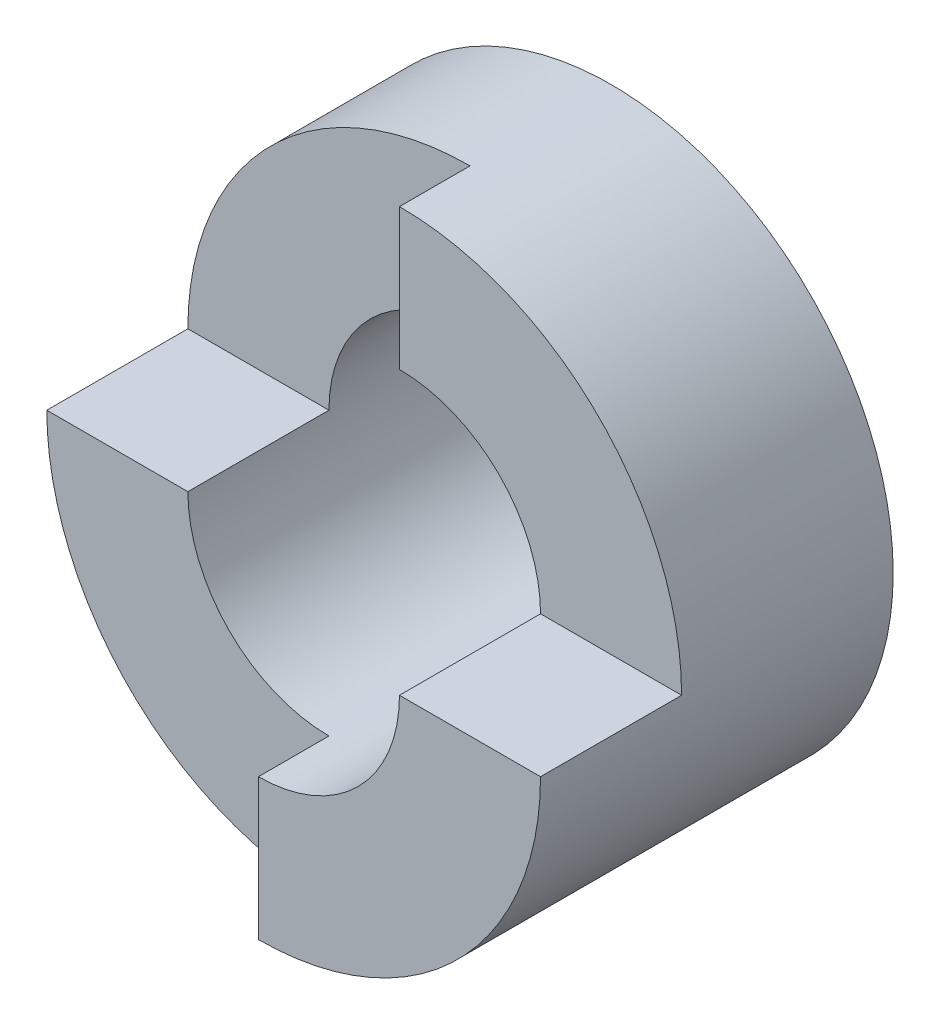
SolidWorks part; units mm, degrees
ref_plane "Front Plane" through (0, 0, 0) normal (0, 0, 1) x (1, 0, 0)
ref_plane "Top Plane" through (0, 0, 0) normal (0, 1, 0) x (1, 0, 0)
ref_plane "Right Plane" through (0, 0, 0) normal (1, 0, 0) x (0, 0, -1)
sketch "Sketch1" plane through (0, 0, 0) normal (0, 0, 1) x (1, 0, 0)
  circle A0 centre (0, 0) radius 4
  circle A1 centre (0, 0) radius 2
  dimension "D1" = 4
  dimension "D2" = 8
extrude "Boss-Extrude1" add sketch "Sketch1" along normal blind 5
sketch "Sketch2" plane through (0, 0, 0) normal (0, 1, 0) x (1, 0, 0)
  line L0 (-4, -2) -> (0, -2)
  line L1 (-4, 0) -> (-4, -5) construction
  line L2 (0, -2) -> (0, -3)
  line L3 (0, -3) -> (4, -3)
  line L4 (4, -5) -> (4, 0) construction
  line L5 (4, -3) -> (4, -5)
  line L6 (4, -5) -> (-4, -5)
  line L7 (-4, -5) -> (-4, -2)
  dimension "D1" = 3
  dimension "D2" = 2
extrude "Cut-Extrude1" cut sketch "Sketch2" along normal blind 5
sketch "Sketch3" plane through (0, 0, 0) normal (0, 1, 0) x (1, 0, 0)
  line L1 (-4, -5) -> (0, -5)
  line L2 (-4, -5) -> (-4, -4)
  line L3 (-4, -4) -> (0, -4)
  line L4 (0, -5) -> (0, -4)
  dimension "D1" = 1
extrude "Cut-Extrude2" cut sketch "Sketch3" against normal blind 5
